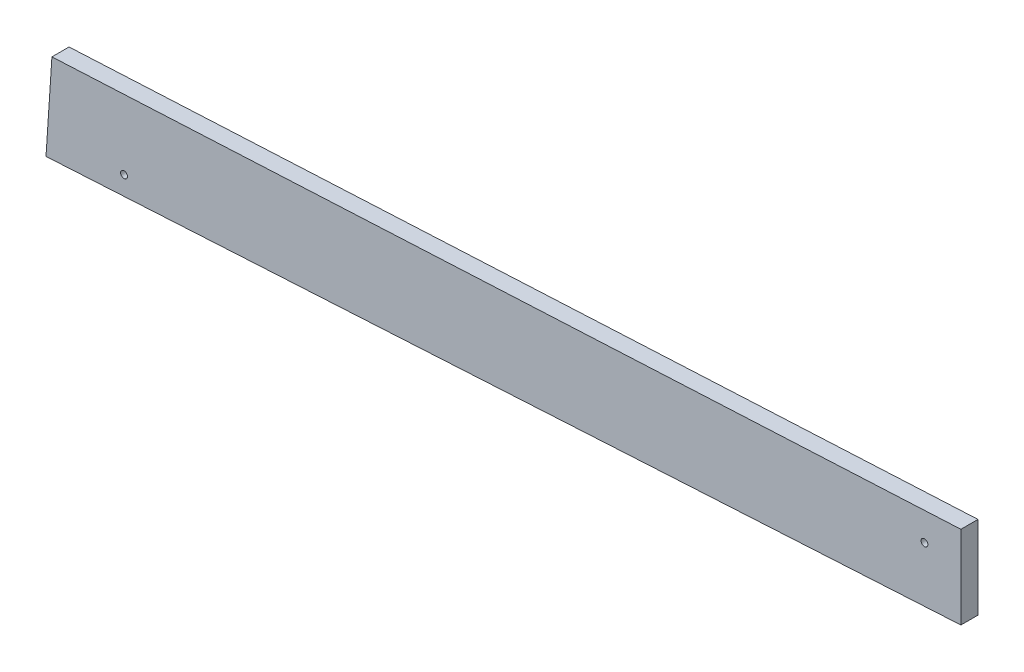
SolidWorks part; units mm, degrees
ref_plane "Front Plane" through (0, 0, 0) normal (0, 0, 1) x (1, 0, 0)
ref_plane "Top Plane" through (0, 0, 0) normal (0, 1, 0) x (1, 0, 0)
ref_plane "Right Plane" through (0, 0, 0) normal (1, 0, 0) x (0, 0, -1)
sketch "Sketch1" plane through (0, 0, 0) normal (0, 0, 1) x (1, 0, 0)
  line L0 (-171.4118, 103.5275) -> (-170.3127, 120.0855) construction
  line L1 (-1.5875, 113.1114) -> (-1.5875, 128.5042) construction
  line L2 (-171.4118, 103.5275) -> (-170.3127, 120.0855)
  line L3 (-1.5875, 113.1114) -> (-1.5875, 128.5042)
  line L4 (-1.5875, 113.1114) -> (-171.4118, 103.5275)
  line L5 (-1.5875, 128.5042) -> (-170.3127, 120.0855)
  circle A0 centre (-8.3466, 122.9689) radius 0.635
  circle A1 centre (-156.9242, 107.8413) radius 0.635
  dimension "D1" = 1.27
  dimension "D2" = 1.27
extrude "Boss-Extrude1" add sketch "Sketch1" against normal blind 3.175 contours L3 L5 L2 L4 A1 A0
